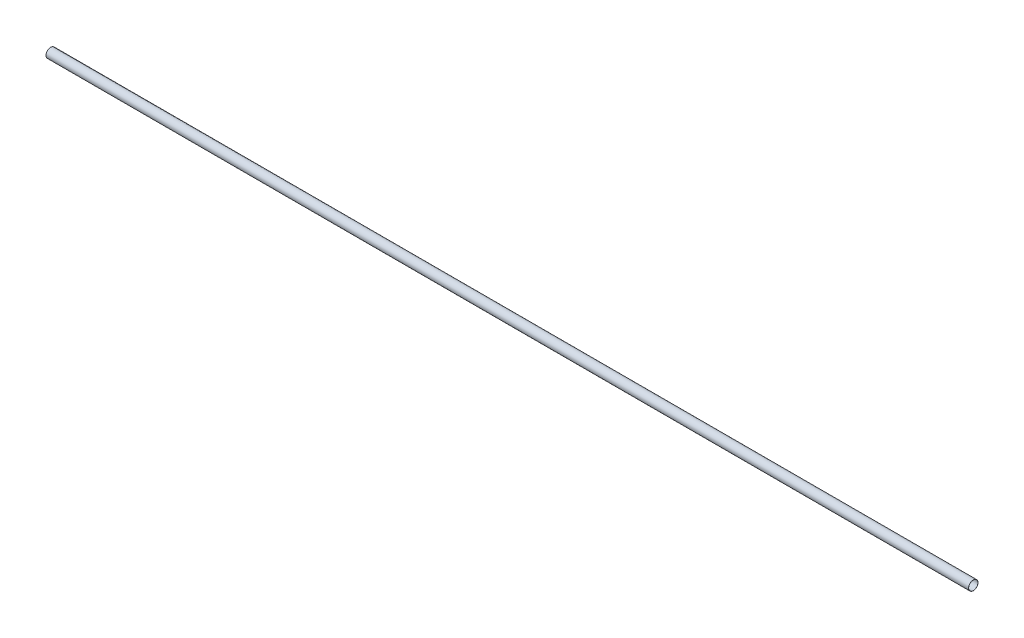
SolidWorks part; units mm, degrees
material "Gray Cast Iron"
ref_plane "Front Plane" through (0, 0, 0) normal (0, 0, 1) x (1, 0, 0)
ref_plane "Top Plane" through (0, 0, 0) normal (0, 1, 0) x (1, 0, 0)
ref_plane "Right Plane" through (0, 0, 0) normal (1, 0, 0) x (0, 0, -1)
sketch "Sketch1" plane through (0, 0, 0) normal (0, 0, 1) x (1, 0, 0)
  line L0 (1, 1) -> (1, 50)
  line L1 (0, 0) -> (10000, 0)
  line L2 (0, 0) -> (0, 51)
  line L3 (0, 51) -> (10000, 51)
  line L4 (10000, 0) -> (10000, 51)
  line L5 (1, 50) -> (9999, 50)
  line L6 (9999, 1) -> (9999, 50)
  line L7 (1, 1) -> (9999, 1)
  dimension "D1" = 51
revolve "Revolve1" add sketch "Sketch1" angle 360 about L3
sketch "Sketch3" plane through (10000, 0, 0) normal (1, 0, 0) x (0, 0, -1)
  circle A0 centre (0, 51) radius 50
extrude "Cut-Extrude1" cut sketch "Sketch3" against normal blind 102101
